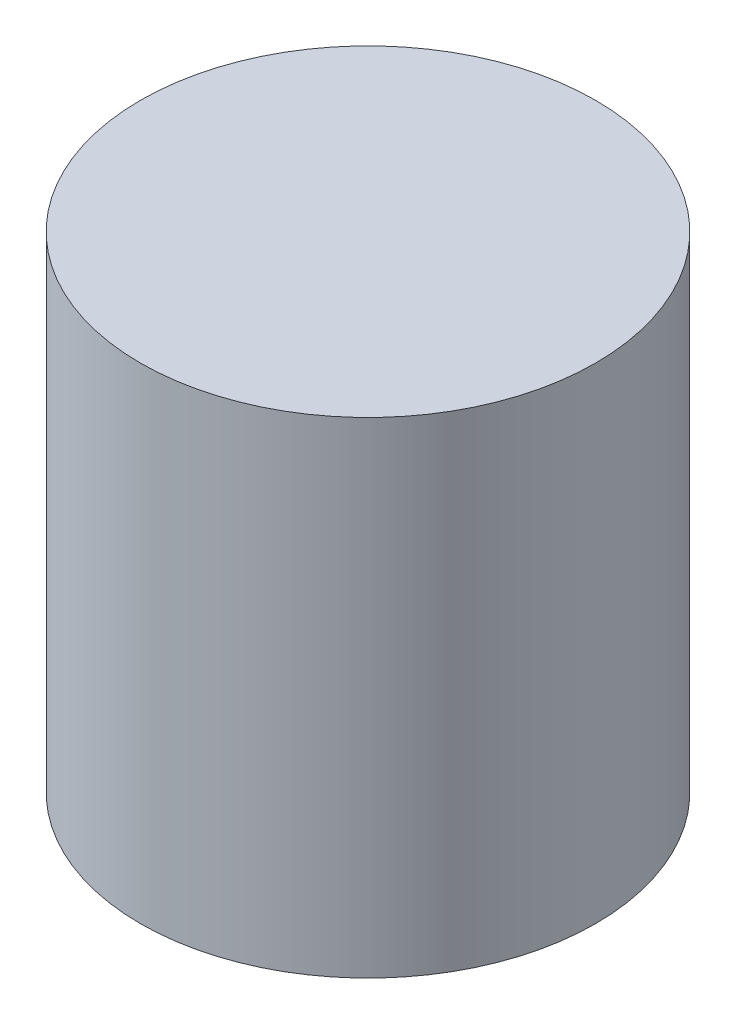
SolidWorks part; units mm, degrees
ref_plane "Front Plane" through (0, 0, 0) normal (0, 0, 1) x (1, 0, 0)
ref_plane "Top Plane" through (0, 0, 0) normal (0, 1, 0) x (1, 0, 0)
ref_plane "Right Plane" through (0, 0, 0) normal (1, 0, 0) x (0, 0, -1)
sketch "Sketch1" plane through (0, 0, 0) normal (0, 1, 0) x (1, 0, 0)
  circle A0 centre (0, 0) radius 37.5
extrude "Boss-Extrude1" add sketch "Sketch1" along normal blind 80
